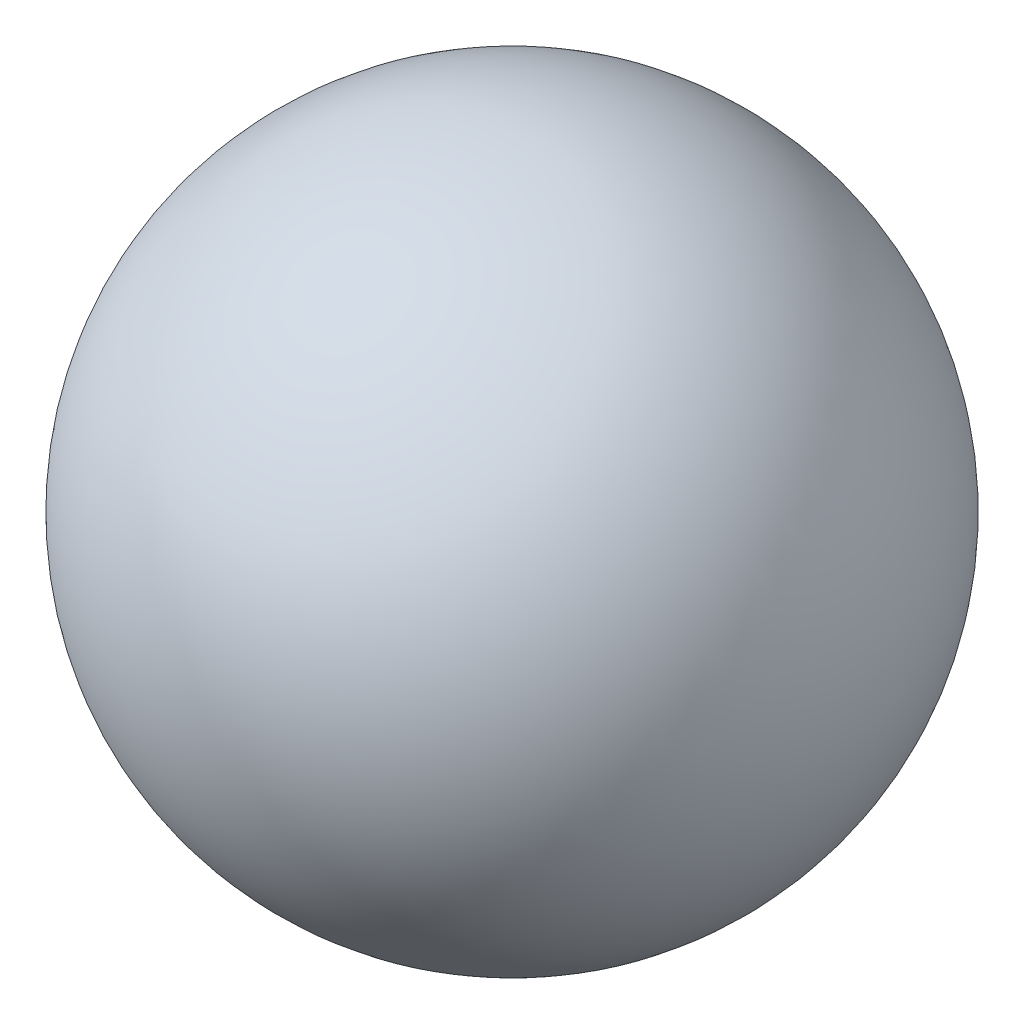
SolidWorks part; units mm, degrees
ref_plane "前视基准面" through (0, 0, 0) normal (0, 0, 1) x (1, 0, 0)
ref_plane "上视基准面" through (0, 0, 0) normal (0, 1, 0) x (1, 0, 0)
ref_plane "右视基准面" through (0, 0, 0) normal (1, 0, 0) x (0, 0, -1)
sketch "草图1" plane through (0, 0, 0) normal (0, 0, 1) x (1, 0, 0)
  line L0 (0, 25) -> (0, -25)
  arc A0 (0, 25) -> (0, -25) centre (0, 0) ccw
revolve "旋转1" add sketch "草图1" angle 360 about L0
